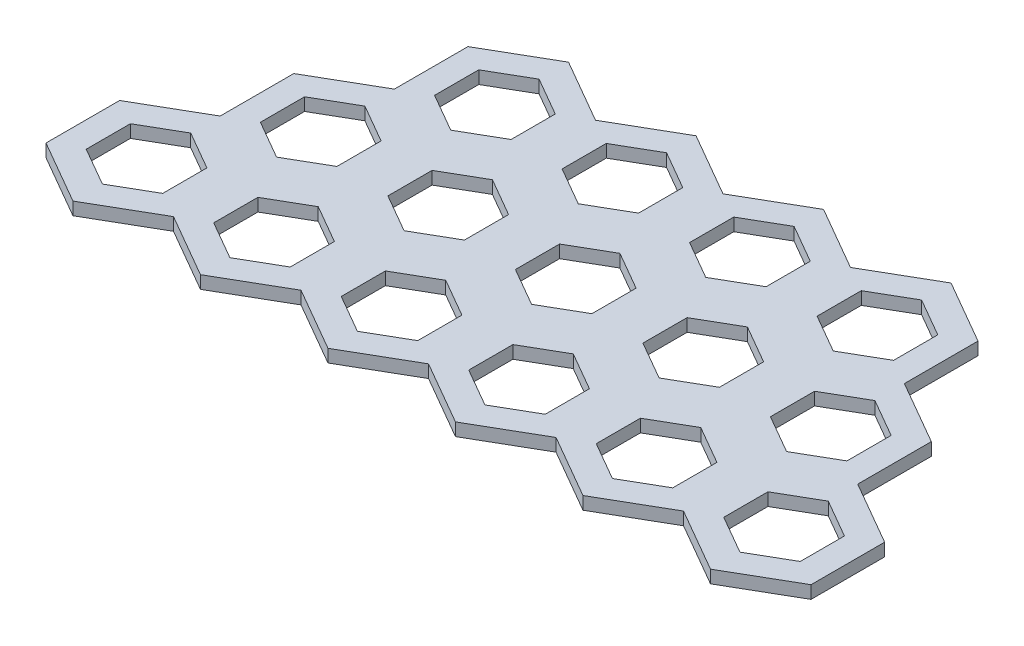
SolidWorks part; units mm, degrees
ref_plane "Front Plane" through (0, 0, 0) normal (0, 0, 1) x (1, 0, 0)
ref_plane "Top Plane" through (0, 0, 0) normal (0, 1, 0) x (1, 0, 0)
ref_plane "Right Plane" through (0, 0, 0) normal (1, 0, 0) x (0, 0, -1)
sketch "Sketch1" plane through (0, 0, 0) normal (0, 1, 0) x (1, 0, 0)
  line L132 (5, 1.7321) -> (3.5, 0.866)
  line L133 (0, 2.8868) -> (-2.5, 1.4434)
  line L134 (-2.5, 1.4434) -> (-2.5, -1.4434)
  line L135 (-2.5, -1.4434) -> (0, -2.8868)
  line L136 (0, -2.8868) -> (2.5, -1.4434)
  line L137 (2.5, -1.4434) -> (2.5, 1.4434)
  line L138 (2.5, 1.4434) -> (0, 2.8868)
  line L139 (0, 1.7321) -> (-1.5, 0.866)
  line L140 (-1.5, 0.866) -> (-1.5, -0.866)
  line L141 (-1.5, -0.866) -> (0, -1.7321)
  line L142 (0, -1.7321) -> (1.5, -0.866)
  line L143 (1.5, -0.866) -> (1.5, 0.866)
  line L144 (1.5, 0.866) -> (0, 1.7321)
  line L145 (3.5, 0.866) -> (3.5, -0.866)
  line L146 (3.5, -0.866) -> (5, -1.7321)
  line L147 (5, -1.7321) -> (6.5, -0.866)
  line L148 (6.5, -0.866) -> (6.5, 0.866)
  line L149 (6.5, 0.866) -> (5, 1.7321)
  line L150 (5, 2.8868) -> (2.5, 1.4434)
  line L151 (2.5, 1.4434) -> (2.5, -1.4434)
  line L152 (2.5, -1.4434) -> (5, -2.8868)
  line L154 (5, -2.8868) -> (7.5, -1.4434)
  line L155 (7.5, -1.4434) -> (7.5, 1.4434)
  line L157 (7.5, 1.4434) -> (5, 2.8868)
  line L158 (10, 1.7321) -> (8.5, 0.866)
  line L159 (8.5, 0.866) -> (8.5, -0.866)
  line L160 (8.5, -0.866) -> (10, -1.7321)
  line L161 (10, -1.7321) -> (11.5, -0.866)
  line L192 (11.5, -0.866) -> (11.5, 0.866)
  line L193 (11.5, 0.866) -> (10, 1.7321)
  line L194 (10, 2.8868) -> (7.5, 1.4434)
  line L195 (7.5, 1.4434) -> (7.5, -1.4434)
  line L196 (7.5, -1.4434) -> (10, -2.8868)
  line L197 (10, -2.8868) -> (12.5, -1.4434)
  line L199 (12.5, -1.4434) -> (12.5, 1.4434)
  line L200 (12.5, 1.4434) -> (10, 2.8868)
  line L201 (15, 1.7321) -> (13.5, 0.866)
  line L202 (13.5, 0.866) -> (13.5, -0.866)
  line L203 (13.5, -0.866) -> (15, -1.7321)
  line L204 (15, -1.7321) -> (16.5, -0.866)
  line L205 (16.5, -0.866) -> (16.5, 0.866)
  line L206 (16.5, 0.866) -> (15, 1.7321)
  line L207 (15, 2.8868) -> (12.5, 1.4434)
  line L208 (12.5, 1.4434) -> (12.5, -1.4434)
  line L211 (12.5, -1.4434) -> (15, -2.8868)
  line L212 (15, -2.8868) -> (17.5, -1.4434)
  line L213 (17.5, -1.4434) -> (17.5, 1.4434)
  line L214 (17.5, 1.4434) -> (15, 2.8868)
  line L215 (2.5, -2.5981) -> (1, -3.4641)
  line L216 (-2.5, -1.4434) -> (-5, -2.8868)
  line L217 (-5, -2.8868) -> (-5, -5.7735)
  line L218 (-5, -5.7735) -> (-2.5, -7.2169)
  line L219 (-2.5, -7.2169) -> (0, -5.7735)
  line L220 (0, -5.7735) -> (0, -2.8868)
  line L223 (0, -2.8868) -> (-2.5, -1.4434)
  line L224 (-2.5, -2.5981) -> (-4, -3.4641)
  line L225 (-4, -3.4641) -> (-4, -5.1962)
  line L226 (-4, -5.1962) -> (-2.5, -6.0622)
  line L227 (-2.5, -6.0622) -> (-1, -5.1962)
  line L228 (-1, -5.1962) -> (-1, -3.4641)
  line L229 (-1, -3.4641) -> (-2.5, -2.5981)
  line L230 (1, -3.4641) -> (1, -5.1962)
  line L231 (1, -5.1962) -> (2.5, -6.0622)
  line L232 (2.5, -6.0622) -> (4, -5.1962)
  line L235 (4, -5.1962) -> (4, -3.4641)
  line L236 (4, -3.4641) -> (2.5, -2.5981)
  line L237 (2.5, -1.4434) -> (0, -2.8868)
  line L239 (0, -2.8868) -> (0, -5.7735)
  line L251 (0, -5.7735) -> (2.5, -7.2169)
  line L263 (2.5, -7.2169) -> (5, -5.7735)
  line L275 (5, -5.7735) -> (5, -2.8868)
  line L287 (5, -2.8868) -> (2.5, -1.4434)
  line L289 (7.5, -2.5981) -> (6, -3.4641)
  line L297 (6, -3.4641) -> (6, -5.1962)
  line L298 (6, -5.1962) -> (7.5, -6.0622)
  line L299 (7.5, -6.0622) -> (9, -5.1962)
  line L300 (9, -5.1962) -> (9, -3.4641)
  line L301 (9, -3.4641) -> (7.5, -2.5981)
  line L302 (7.5, -1.4434) -> (5, -2.8868)
  line L303 (5, -2.8868) -> (5, -5.7735)
  line L304 (5, -5.7735) -> (7.5, -7.2169)
  line L305 (7.5, -7.2169) -> (10, -5.7735)
  line L306 (10, -5.7735) -> (10, -2.8868)
  line L307 (10, -2.8868) -> (7.5, -1.4434)
  line L308 (12.5, -2.5981) -> (11, -3.4641)
  line L309 (11, -3.4641) -> (11, -5.1962)
  line L310 (11, -5.1962) -> (12.5, -6.0622)
  line L311 (12.5, -6.0622) -> (14, -5.1962)
  line L312 (14, -5.1962) -> (14, -3.4641)
  line L313 (14, -3.4641) -> (12.5, -2.5981)
  line L314 (12.5, -1.4434) -> (10, -2.8868)
  line L315 (10, -2.8868) -> (10, -5.7735)
  line L316 (10, -5.7735) -> (12.5, -7.2169)
  line L317 (12.5, -7.2169) -> (15, -5.7735)
  line L318 (15, -5.7735) -> (15, -2.8868)
  line L319 (15, -2.8868) -> (12.5, -1.4434)
  line L320 (17.5, -2.5981) -> (16, -3.4641)
  line L321 (16, -3.4641) -> (16, -5.1962)
  line L322 (16, -5.1962) -> (17.5, -6.0622)
  line L323 (17.5, -6.0622) -> (19, -5.1962)
  line L324 (19, -5.1962) -> (19, -3.4641)
  line L325 (19, -3.4641) -> (17.5, -2.5981)
  line L326 (17.5, -1.4434) -> (15, -2.8868)
  line L327 (15, -2.8868) -> (15, -5.7735)
  line L328 (15, -5.7735) -> (17.5, -7.2169)
  line L329 (17.5, -7.2169) -> (20, -5.7735)
  line L330 (20, -5.7735) -> (20, -2.8868)
  line L331 (20, -2.8868) -> (17.5, -1.4434)
  line L332 (0, -6.9282) -> (-1.5, -7.7942)
  line L333 (-5, -5.7735) -> (-7.5, -7.2169)
  line L334 (-7.5, -7.2169) -> (-7.5, -10.1036)
  line L335 (-7.5, -10.1036) -> (-5, -11.547)
  line L336 (-5, -11.547) -> (-2.5, -10.1036)
  line L337 (-2.5, -10.1036) -> (-2.5, -7.2169)
  line L338 (-2.5, -7.2169) -> (-5, -5.7735)
  line L339 (-5, -6.9282) -> (-6.5, -7.7942)
  line L340 (-6.5, -7.7942) -> (-6.5, -9.5263)
  line L341 (-6.5, -9.5263) -> (-5, -10.3923)
  line L342 (-5, -10.3923) -> (-3.5, -9.5263)
  line L343 (-3.5, -9.5263) -> (-3.5, -7.7942)
  line L344 (-3.5, -7.7942) -> (-5, -6.9282)
  line L345 (-1.5, -7.7942) -> (-1.5, -9.5263)
  line L346 (-1.5, -9.5263) -> (0, -10.3923)
  line L347 (0, -10.3923) -> (1.5, -9.5263)
  line L348 (1.5, -9.5263) -> (1.5, -7.7942)
  line L349 (1.5, -7.7942) -> (0, -6.9282)
  line L350 (0, -5.7735) -> (-2.5, -7.2169)
  line L351 (-2.5, -7.2169) -> (-2.5, -10.1036)
  line L352 (-2.5, -10.1036) -> (0, -11.547)
  line L353 (0, -11.547) -> (2.5, -10.1036)
  line L354 (2.5, -10.1036) -> (2.5, -7.2169)
  line L355 (2.5, -7.2169) -> (0, -5.7735)
  line L356 (5, -6.9282) -> (3.5, -7.7942)
  line L357 (3.5, -7.7942) -> (3.5, -9.5263)
  line L358 (3.5, -9.5263) -> (5, -10.3923)
  line L359 (5, -10.3923) -> (6.5, -9.5263)
  line L360 (6.5, -9.5263) -> (6.5, -7.7942)
  line L361 (6.5, -7.7942) -> (5, -6.9282)
  line L362 (5, -5.7735) -> (2.5, -7.2169)
  line L363 (2.5, -7.2169) -> (2.5, -10.1036)
  line L364 (2.5, -10.1036) -> (5, -11.547)
  line L365 (5, -11.547) -> (7.5, -10.1036)
  line L366 (7.5, -10.1036) -> (7.5, -7.2169)
  line L367 (7.5, -7.2169) -> (5, -5.7735)
  line L368 (10, -6.9282) -> (8.5, -7.7942)
  line L369 (8.5, -7.7942) -> (8.5, -9.5263)
  line L370 (8.5, -9.5263) -> (10, -10.3923)
  line L371 (10, -10.3923) -> (11.5, -9.5263)
  line L372 (11.5, -9.5263) -> (11.5, -7.7942)
  line L373 (11.5, -7.7942) -> (10, -6.9282)
  line L374 (10, -5.7735) -> (7.5, -7.2169)
  line L375 (7.5, -7.2169) -> (7.5, -10.1036)
  line L376 (7.5, -10.1036) -> (10, -11.547)
  line L377 (10, -11.547) -> (12.5, -10.1036)
  line L378 (12.5, -10.1036) -> (12.5, -7.2169)
  line L379 (12.5, -7.2169) -> (10, -5.7735)
  line L380 (15, -6.9282) -> (13.5, -7.7942)
  line L381 (13.5, -7.7942) -> (13.5, -9.5263)
  line L382 (13.5, -9.5263) -> (15, -10.3923)
  line L383 (15, -10.3923) -> (16.5, -9.5263)
  line L384 (16.5, -9.5263) -> (16.5, -7.7942)
  line L385 (16.5, -7.7942) -> (15, -6.9282)
  line L386 (15, -5.7735) -> (12.5, -7.2169)
  line L387 (12.5, -7.2169) -> (12.5, -10.1036)
  line L388 (12.5, -10.1036) -> (15, -11.547)
  line L389 (15, -11.547) -> (17.5, -10.1036)
  line L390 (17.5, -10.1036) -> (17.5, -7.2169)
  line L391 (17.5, -7.2169) -> (15, -5.7735)
  line L392 (20, -6.9282) -> (18.5, -7.7942)
  line L393 (18.5, -7.7942) -> (18.5, -9.5263)
  line L394 (18.5, -9.5263) -> (20, -10.3923)
  line L395 (20, -10.3923) -> (21.5, -9.5263)
  line L396 (21.5, -9.5263) -> (21.5, -7.7942)
  line L397 (21.5, -7.7942) -> (20, -6.9282)
  line L398 (20, -5.7735) -> (17.5, -7.2169)
  line L399 (17.5, -7.2169) -> (17.5, -10.1036)
  line L400 (17.5, -10.1036) -> (20, -11.547)
  line L401 (20, -11.547) -> (22.5, -10.1036)
  line L402 (22.5, -10.1036) -> (22.5, -7.2169)
  line L403 (22.5, -7.2169) -> (20, -5.7735)
  circle A0 centre (0, 0) radius 2.5 construction
  circle A1 centre (0, 0) radius 1.5 construction
  circle A2 centre (-2.5, -4.3301) radius 2.5 construction
  circle A3 centre (-2.5, -4.3301) radius 1.5 construction
  circle A4 centre (-5, -8.6603) radius 2.5 construction
  circle A5 centre (-5, -8.6603) radius 1.5 construction
  dimension "D1" = 3
  dimension "D2" = 5
  dimension "D4" = 5
  dimension "D5" = 3
  dimension "D7" = 3
  dimension "D8" = 5
  dimension "D3" = 4
  dimension "D6" = 5
  dimension "D9" = 6
extrude "Boss-Extrude2" add sketch "Sketch1" along normal blind 0.5 contours L219 L220 L135 L216 L217 L218 L229 L228 L227 L226 L225 L224 | L336 L337 L218 L333 L334 L335 L344 L343 L342 L341 L340 L339 | L353 L354 L251 L219 L337 L352 L349 L348 L347 L346 L345 L332 | L365 L366 L304 L263 L354 L364 L361 L360 L359 L358 L357 L356 | L263 L275 L152 L136 L220 L251 L236 L235 L232 L231 L230 L215 | L137 L138 L133 L134 L135 L136 L144 L143 L142 L141 L140 L139 | L155 L157 L150 L137 L152 L154 L149 L148 L147 L146 L145 L132 | L305 L306 L196 L154 L275 L304 L301 L300 L299 L298 L297 L289 | L377 L378 L316 L305 L366 L376 L373 L372 L371 L370 L369 L368 | L402 L403 L329 L390 L400 L401 L397 L396 L395 L394 L393 L392 | L389 L390 L328 L317 L378 L388 L385 L384 L383 L382 L381 L380 | L330 L331 L212 L318 L328 L329 L325 L324 L323 L322 L321 L320 | L317 L318 L211 L197 L306 L316 L313 L312 L311 L310 L309 L308 | L213 L214 L207 L199 L211 L212 L206 L205 L204 L203 L202 L201 | L199 L200 L194 L155 L196 L197 L193 L192 L161 L160 L159 L158
